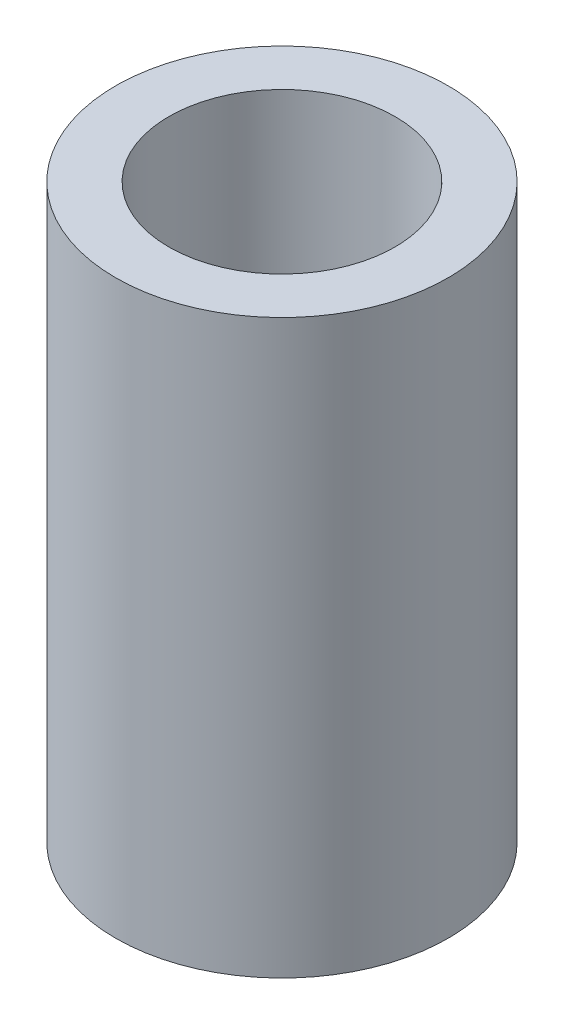
SolidWorks part; units mm, degrees
ref_plane "Alzado" through (0, 0, 0) normal (0, 0, 1) x (1, 0, 0)
ref_plane "Planta" through (0, 0, 0) normal (0, 1, 0) x (1, 0, 0)
ref_plane "Vista lateral" through (0, 0, 0) normal (1, 0, 0) x (0, 0, -1)
sketch "Croquis1" plane through (0, 0, 0) normal (0, 1, 0) x (1, 0, 0)
  circle A0 centre (0, 0) radius 6.25
  circle A1 centre (0, 0) radius 4.25
  dimension "D1" = 8.5
  dimension "D2" = 2
  dimension "D3" = 12.5
extrude "Saliente-Extruir1" add sketch "Croquis1" along normal blind 21.5
